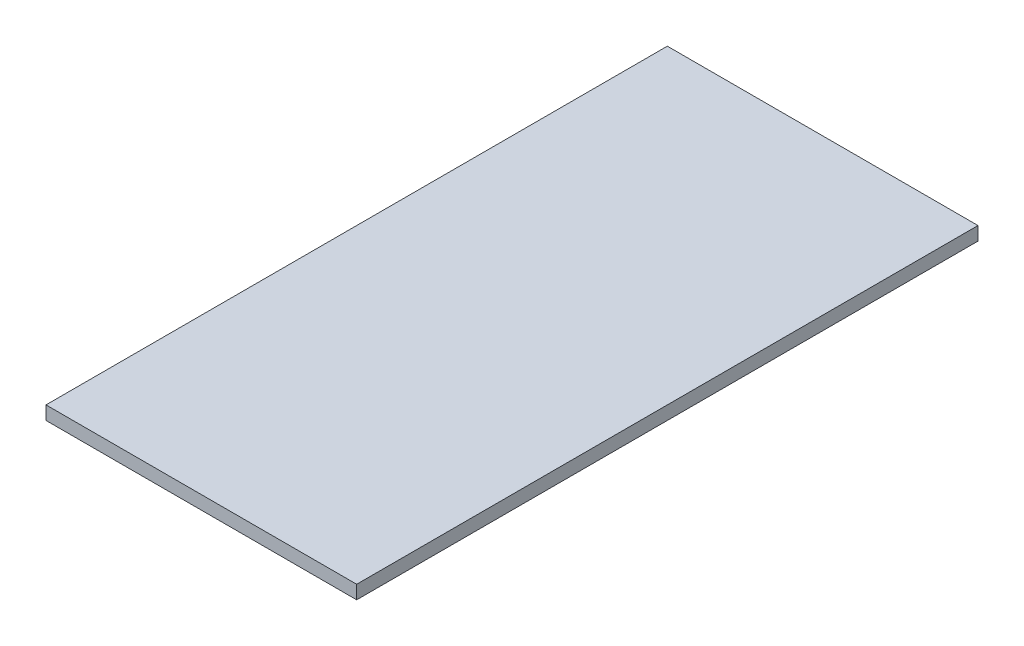
SolidWorks part; units mm, degrees
ref_plane "Front Plane" through (0, 0, 0) normal (0, 0, 1) x (1, 0, 0)
ref_plane "Top Plane" through (0, 0, 0) normal (0, 1, 0) x (1, 0, 0)
ref_plane "Right Plane" through (0, 0, 0) normal (1, 0, 0) x (0, 0, -1)
sketch "Sketch1" plane through (0, 0, 0) normal (0, 1, 0) x (1, 0, 0)
  line L0 (0, 0) -> (0, -115) construction
  line L1 (-57.5, 115) -> (57.5, 115)
  line L2 (-57.5, 115) -> (-57.5, -115)
  line L3 (-57.5, -115) -> (57.5, -115)
  line L4 (57.5, 115) -> (57.5, -115)
  line L5 (0, 0) -> (-57.5, 0) construction
  point P7 (-57.5, 0)
  dimension "D1" = 115
  dimension "D2" = 230
extrude "Boss-Extrude1" add sketch "Sketch1" along normal blind 5 contours L4 L3 L2 L1
